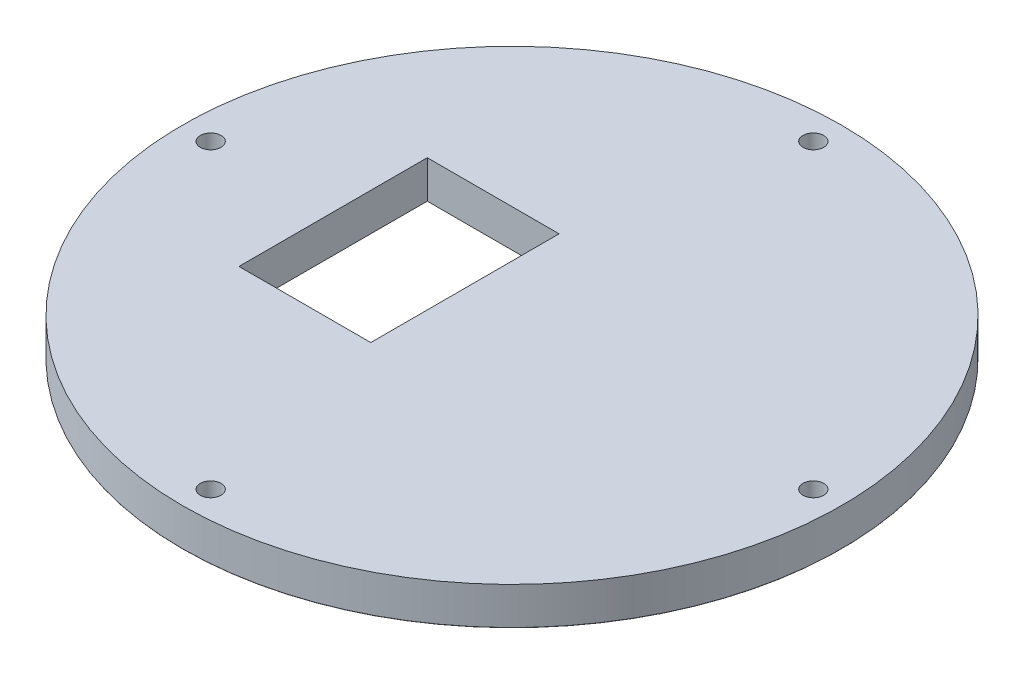
SolidWorks part; units mm, degrees
ref_plane "Front Plane" through (0, 0, 0) normal (0, 0, 1) x (1, 0, 0)
ref_plane "Top Plane" through (0, 0, 0) normal (0, 1, 0) x (1, 0, 0)
ref_plane "Right Plane" through (0, 0, 0) normal (1, 0, 0) x (0, 0, -1)
sketch "Sketch1" plane through (0, 0, 0) normal (0, 1, 0) x (1, 0, 0)
  circle A0 centre (0, 0) radius 87.5
  dimension "D1" = 175
extrude "Boss-Extrude1" add sketch "Sketch1" along normal blind 10
sketch "Sketch2" plane through (0, 10, 0) normal (0, 1, 0) x (1, 0, 0)
  circle A0 centre (0, -80) radius 7.5
  circle A1 centre (-80, 0) radius 7.5
  circle A2 centre (0, 80) radius 7.5
  circle A3 centre (80, 0) radius 7.5
  circle A4 centre (0, 0) radius 87.5 construction
  dimension "D1" = 15
extrude "Boss-Extrude2" add sketch "Sketch2" along normal blind 80
sketch "Sketch3" plane through (0, 0, 0) normal (0, -1, 0) x (-1, 0, 0)
  circle A0 centre (-80, 0) radius 7.5 construction
  circle A1 centre (0, 80) radius 7.5 construction
  circle A2 centre (80, 0) radius 7.5 construction
  circle A3 centre (0, -80) radius 7.5 construction
  point P0 (-80, 0)
  point P2 (0, 80)
  point P4 (80, 0)
  point P6 (0, -80)
hole_wizard "CBORE for M5 Hex Head Bolt1" positions "Sketch3" profile "Sketch4" counterbore size "M5" standard "ANSI Metric"
sketch "Sketch4" plane through (80, 0, 0) normal (1, 0, 0) x (0, 0, -1)
  line L0 (0, 0) -> (0, 21.6524)
  line L1 (0, 21.6524) -> (2.75, 20)
  line L2 (2.75, 20) -> (2.75, 3.58)
  line L3 (2.75, 3.58) -> (6.12, 3.58)
  line L5 (6.12, 3.58) -> (6.12, 0.025)
  line L6 (6.12, 0.025) -> (6.145, 0)
  line L7 (6.145, 0) -> (0, 0)
  line L8 (-6.12, 0.025) -> (-6.145, 0) construction
  line L10 (0, 21.6524) -> (-2.75, 20) construction
  line L11 (0, -6.35) -> (0, 107.95) construction
  dimension "Hole Dia." = 5.5
  dimension "Hole Depth" = 20
  dimension "C'Bore Dia." = 12.24
  dimension "C'Bore Depth" = 3.58
  dimension "Near C'Sink Dia." = 12.29
  dimension "Near C'Sink Angle" = 90
  dimension "Drill Angle" = 118
sketch "Sketch5" plane through (0, 10, 0) normal (0, 1, 0) x (1, 0, 0)
  circle A0 centre (0, 0) radius 87.5
  arc A1 (0, 87.5) -> (-87.5, 0) centre (0, 0) ccw construction
extrude "Cut-Extrude1" cut sketch "Sketch5" along normal blind 80
fillet "Fillet1" radius 0.1 1 edges at (0, 0, 87.5)
sketch "Sketch10" plane through (0, 10, 0) normal (0, 1, 0) x (1, 0, 0)
  line L1 (-47.5, -25) -> (-12.5, -25)
  line L2 (-47.5, -25) -> (-47.5, 25)
  line L3 (-47.5, 25) -> (-12.5, 25)
  line L4 (-12.5, -25) -> (-12.5, 25)
  line L5 (-47.5, -25) -> (-12.5, 25) construction
  line L6 (-47.5, 25) -> (-12.5, -25) construction
  point P0 (-30, 0)
  dimension "D1" = 35
  dimension "D2" = 50
  dimension "D3" = 30
extrude "Cut-Extrude3" cut sketch "Sketch10" against normal blind 23
sketch "Sketch12" plane through (0, 0, 0) normal (0, -1, 0) x (1, 0, 0)
  line L0 (22.5, 4.7) -> (22.5, 11.3) construction
  line L1 (22.5, 16) -> (17.5, 16)
  line L2 (22.5, 16) -> (22.5, -16)
  line L3 (22.5, -16) -> (17.5, -16)
  line L4 (-9.5, 16) -> (-9.5, -16)
  line L6 (-9.5, 11.3) -> (-9.5, 4.7) construction
  line L7 (-7.5, 16) -> (-4.5, 16) construction
  line L8 (-7.5, -16) -> (-5.95, -16) construction
  line L9 (-12.5, 25) -> (-12.5, -25) construction
  line L10 (25.5, 19) -> (-12.5, 19)
  line L11 (25.5, 19) -> (25.5, -19)
  line L12 (25.5, -19) -> (-12.5, -19)
  line L13 (-12.5, 19) -> (-12.5, -19)
  line L16 (17.5, 16) -> (17.5, 13)
  line L17 (17.5, 13) -> (-4.5, 13)
  line L18 (-4.5, 16) -> (-4.5, 13)
  line L19 (-4.5, 14.5) -> (-4.5, 12.618) construction
  line L20 (17.5, 12.618) -> (17.5, 14.5) construction
  line L23 (17.5, -16) -> (17.5, -13)
  line L24 (17.5, -13) -> (-4.5, -13)
  line L25 (-4.5, -16) -> (-4.5, -13)
  line L27 (17.5, -13) -> (17.5, -16) construction
  line L28 (-4.5, -12.618) -> (-4.5, -14.5) construction
  line L29 (-4.5, 16) -> (-9.5, 16)
  line L30 (-4.5, -16) -> (-9.5, -16)
  dimension "D1" = 3
  dimension "D2" = 3
  dimension "D3" = 3
  dimension "D4" = 3
  dimension "D5" = 3
extrude "Boss-Extrude3" add sketch "Sketch12" along normal up to surface (6 mm away)
sketch "Sketch13" plane through (0, -6, 0) normal (0, -1, 0) x (1, 0, 0)
  line L0 (25.5, 19) -> (-12.5, 19) construction
  line L1 (17.5, 13) -> (-4.5, 13)
  line L2 (17.5, 13) -> (17.5, 19)
  line L3 (17.5, 19) -> (-4.5, 19)
  line L4 (-4.5, 13) -> (-4.5, 19)
  line L5 (-4.5, 13) -> (-4.5, 16) construction
  line L6 (-12.5, -19) -> (25.5, -19) construction
  line L7 (17.5, -13) -> (-4.5, -13)
  line L8 (17.5, -13) -> (17.5, -19)
  line L9 (17.5, -19) -> (-4.5, -19)
  line L10 (-4.5, -13) -> (-4.5, -19)
  line L11 (-4.5, -16) -> (-4.5, -13) construction
extrude "Boss-Extrude4" add sketch "Sketch13" along normal blind 15
sketch "Sketch14" plane through (0, -6, 0) normal (0, -1, 0) x (1, 0, 0)
  line L0 (25.5, -19) -> (25.5, 19) construction
  line L1 (25.5, 4) -> (22.5, 4)
  line L2 (25.5, 4) -> (25.5, -4)
  line L3 (25.5, -4) -> (22.5, -4)
  line L4 (22.5, 4) -> (22.5, -4)
  line L5 (22.5, -16) -> (22.5, 16) construction
  line L6 (24.7, 4) -> (22.5, 4) construction
  line L7 (24.7, -4) -> (22.5, -4) construction
extrude "Boss-Extrude5" add sketch "Sketch14" along normal blind 13
sketch "Sketch15" plane through (-4.5, 0, 0) normal (-1, 0, 0) x (0, 0, 1)
  arc A0 (-13.5, -17.1) -> (-13.5, -14.9) centre (-13.5, -16) ccw construction
  arc A1 (-13.5, -14.9) -> (-13.5, -17.1) centre (-13.5, -16) ccw construction
  arc A2 (13.5, -17.1) -> (13.5, -14.9) centre (13.5, -16) ccw construction
  arc A3 (13.5, -14.9) -> (13.5, -17.1) centre (13.5, -16) ccw construction
  arc A4 (-13.5, -17.1) -> (-13.5, -14.9) centre (-13.5, -16) ccw
  arc A5 (-13.5, -14.9) -> (-13.5, -17.1) centre (-13.5, -16) ccw
  arc A6 (13.5, -17.1) -> (13.5, -14.9) centre (13.5, -16) ccw
  arc A7 (13.5, -14.9) -> (13.5, -17.1) centre (13.5, -16) ccw
extrude "Cut-Extrude4" cut sketch "Sketch15" against normal through all
